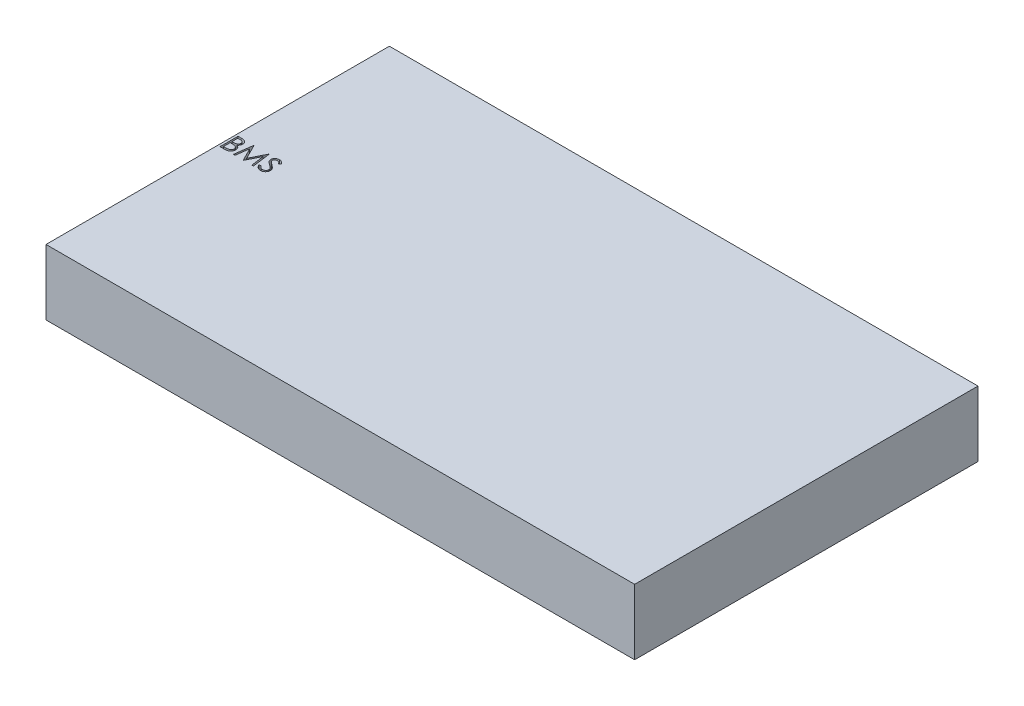
SolidWorks part; units mm, degrees
ref_plane "Front Plane" through (0, 0, 0) normal (0, 0, 1) x (1, 0, 0)
ref_plane "Top Plane" through (0, 0, 0) normal (0, 1, 0) x (1, 0, 0)
ref_plane "Right Plane" through (0, 0, 0) normal (1, 0, 0) x (0, 0, -1)
sketch "Sketch1" plane through (0, 0, 0) normal (0, 1, 0) x (1, 0, 0)
  line L1 (0, 0) -> (114.3, 0)
  line L2 (0, 0) -> (0, 66.675)
  line L3 (0, 66.675) -> (114.3, 66.675)
  line L4 (114.3, 0) -> (114.3, 66.675)
  dimension "D1" = 66.675
  dimension "D2" = 114.3
extrude "Boss-Extrude1" add sketch "Sketch1" along normal blind 12.7
sketch "Sketch2" plane through (0, 12.7, 0) normal (0, 1, 0) x (1, 0, 0)
  line L0 (0, 33.3375) -> (114.3, 33.3375) construction
  line L1 (0, 66.675) -> (0, 0) construction
  line L2 (114.3, 0) -> (114.3, 66.675) construction
  text T0 "BMS"
extrude "Cut-Extrude1" cut sketch "Sketch2" against normal through all
